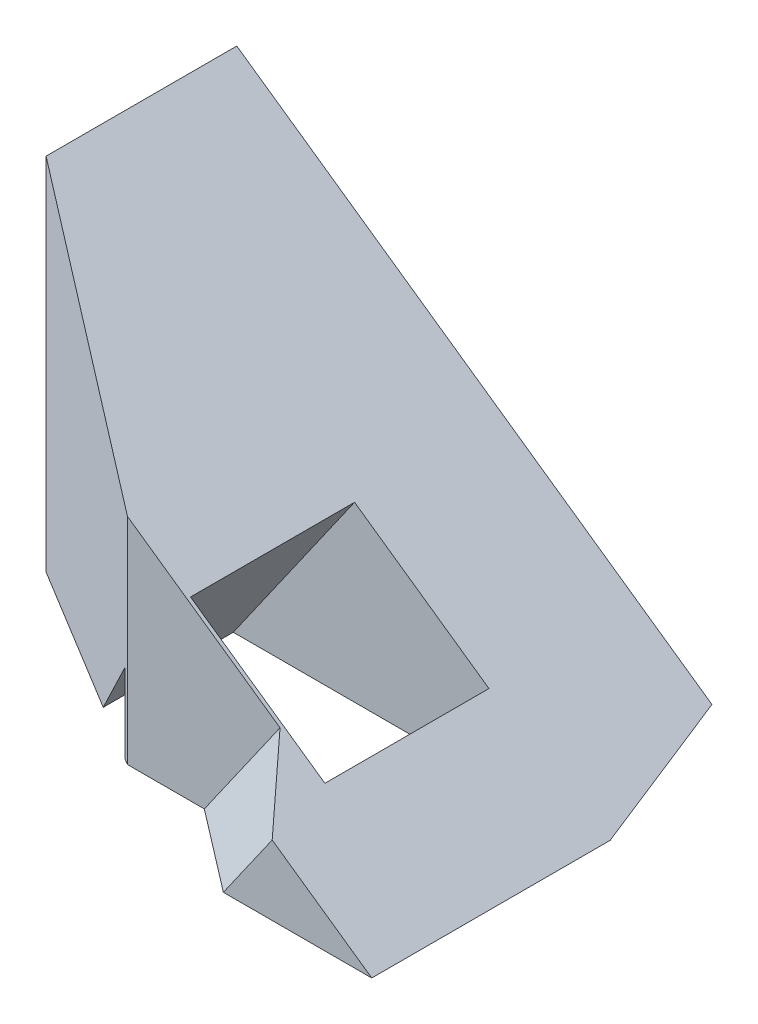
SolidWorks part; units mm, degrees
ref_plane "Ebene vorne" through (0, 0, 0) normal (0, 0, 1) x (1, 0, 0)
ref_plane "Ebene oben" through (0, 0, 0) normal (0, 1, 0) x (1, 0, 0)
ref_plane "Ebene rechts" through (0, 0, 0) normal (1, 0, 0) x (0, 0, -1)
sketch "Skizze1" plane through (0, 0, 0) normal (0, 1, 0) x (1, 0, 0)
  line L1 (0, 0) -> (100, 0)
  line L2 (0, 0) -> (0, 100)
  line L3 (0, 100) -> (100, 100)
  line L4 (100, 0) -> (100, 100)
  dimension "D1" = 100
  dimension "D2" = 100
extrude "Aufsatz-Linear austragen1" add sketch "Skizze1" along normal blind 50
sketch "Skizze2" plane through (0, 0, 0) normal (0, 0, 1) x (1, 0, 0)
  line L0 (0, 0) -> (0, 70.0208)
  line L1 (0, 50) -> (0, 0) construction
  line L2 (0, 70.0208) -> (100, 0)
  line L3 (100, 50) -> (100, 0) construction
  line L4 (0, 0) -> (100, 0) construction
  line L5 (100, 0) -> (0, 0)
  dimension "D1" = 35
extrude "Schnitt-Linear austragen1" cut sketch "Skizze2" against normal through all flip side to cut
sketch "Skizze3" plane through (32.899, 46.9846, 0) normal (0.5736, 0.8192, 0) x (0.8192, -0.5736, 0)
  line L0 (81.9152, 37.8599) -> (81.9152, 55.3003)
  line L1 (81.9152, 55.3003) -> (78.4081, 65.6148)
  line L2 (78.4081, 65.6148) -> (35.9841, 65.6148)
  line L3 (81.9152, 0) -> (81.9152, 100) construction
  line L5 (59.8285, 42.6962) -> (71.8285, 42.6962)
  line L6 (35.9841, 65.6148) -> (35.9841, 51.6641)
  line L7 (35.9841, 51.6641) -> (54.5019, 42.4462)
  line L8 (54.5019, 42.4462) -> (68.1285, 42.4462)
  line L9 (68.1285, 42.4462) -> (73.0257, 37.8599)
  line L10 (73.0257, 37.8599) -> (81.9152, 37.8599)
  line L11 (59.8285, 42.6962) -> (59.8285, 54.6962)
  line L12 (59.8285, 54.6962) -> (71.8285, 54.6962)
  line L13 (71.8285, 42.6962) -> (71.8285, 54.6962)
  dimension "D1" = 12
  dimension "D2" = 12
  dimension "D3" = 8.3
  dimension "D4" = 0.25
extrude "Schnitt-Linear austragen2" cut sketch "Skizze3" against normal through all flip side to cut
sketch "Skizze4" plane through (0, 0, 0) normal (0, 1, 0) x (1, 0, 0)
  line L0 (62.3755, 51.6641) -> (77.5443, 42.4462) construction
  line L1 (62.3755, 65.6148) -> (62.3755, 51.6641) construction
  line L2 (62.3755, 65.6148) -> (62.3755, 51.6641)
  line L3 (28.3866, 16.7479) -> (62.3755, 16.7479)
  line L4 (28.3866, 16.7479) -> (28.3866, 99.8905)
  line L5 (28.3866, 99.8905) -> (62.3755, 99.8905)
  line L6 (62.3755, 99.8905) -> (62.3755, 65.6148)
  line L7 (62.3755, 51.6641) -> (77.5443, 42.4462)
  line L8 (77.5443, 42.4462) -> (62.3755, 16.7479)
extrude "Schnitt-Linear austragen3" cut sketch "Skizze4" along normal blind 50
